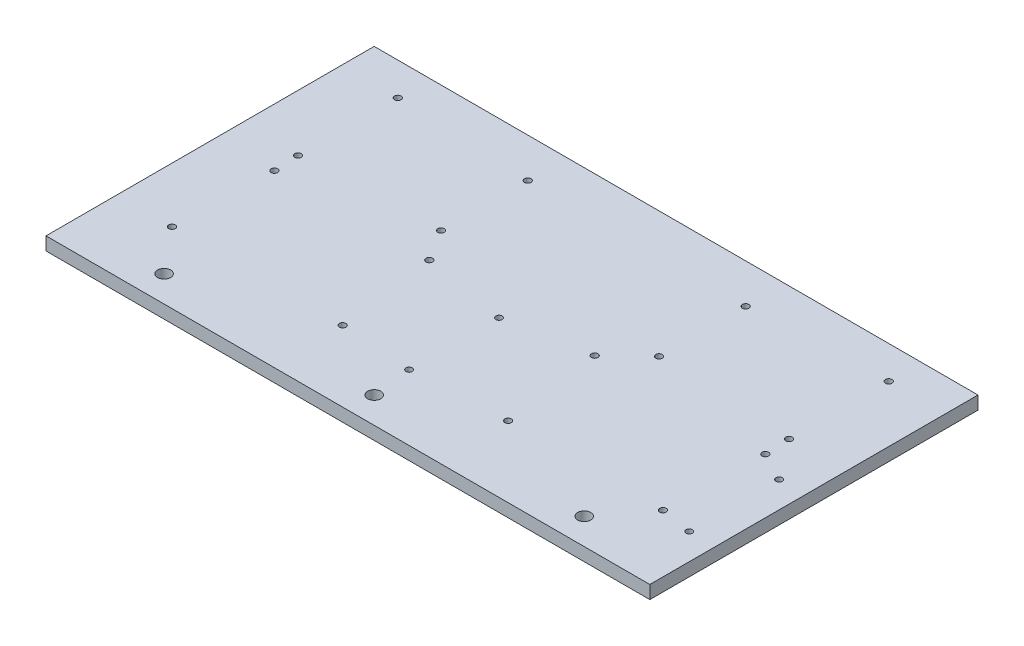
SolidWorks part; units mm, degrees
ref_plane "Front Plane" through (0, 0, 0) normal (0, 0, 1) x (1, 0, 0)
ref_plane "Top Plane" through (0, 0, 0) normal (0, 1, 0) x (1, 0, 0)
ref_plane "Right Plane" through (0, 0, 0) normal (1, 0, 0) x (0, 0, -1)
sketch "Sketch1" plane through (0, 0, 0) normal (0, 1, 0) x (1, 0, 0)
  line L1 (0, 0) -> (292.1, 0)
  line L2 (0, 0) -> (0, 158.75)
  line L3 (0, 158.75) -> (292.1, 158.75)
  line L4 (292.1, 0) -> (292.1, 158.75)
  dimension "D1" = 292.1
  dimension "D2" = 158.75
extrude "Boss-Extrude1" add sketch "Sketch1" along normal blind 6.35
sketch "Sketch2" plane through (0, 6.35, 0) normal (0, 1, 0) x (1, 0, 0)
  line L0 (0, 25.4) -> (292.1, 25.4) construction
  line L1 (0, 12.7) -> (292.1, 12.7) construction
  line L2 (146.05, 0) -> (146.05, 158.75) construction
  line L4 (0, 158.75) -> (0, 0)
  line L5 (0, 0) -> (292.1, 0)
  line L6 (292.1, 0) -> (292.1, 158.75)
  line L7 (292.1, 158.75) -> (0, 158.75)
  line L8 (0, 158.75) -> (0, 0) construction
  line L9 (0, 0) -> (292.1, 0) construction
  line L10 (292.1, 0) -> (292.1, 158.75) construction
  line L11 (292.1, 158.75) -> (0, 158.75) construction
  circle A0 centre (146.05, 12.7) radius 3.175
  circle A1 centre (247.65, 12.7) radius 3.175
  circle A2 centre (44.45, 12.7) radius 3.175
  dimension "D6" = 6.35
  dimension "D7" = 6.35
  dimension "D8" = 6.35
  dimension "D2" = 25.4
  dimension "D3" = 12.7
  dimension "D4" = 101.6
  dimension "D5" = 101.6
  dimension "D1" = 0
extrude "Cut-Extrude2" cut sketch "Sketch2" against normal blind 6.35
sketch "Sketch4" plane through (0, 6.35, 0) normal (0, 1, 0) x (1, 0, 0)
  line L4 (279.4, 85.09) -> (177.8, 85.09)
  line L5 (177.8, 85.09) -> (177.8, 31.75)
  line L6 (177.8, 31.75) -> (279.4, 31.75)
  line L7 (279.4, 31.75) -> (279.4, 85.09)
  line L8 (279.4, 85.09) -> (177.8, 85.09) construction
  line L9 (177.8, 85.09) -> (177.8, 31.75) construction
  line L10 (177.8, 31.75) -> (279.4, 31.75) construction
  line L11 (279.4, 31.75) -> (279.4, 85.09) construction
  line L160 (114.3, 31.75) -> (114.3, 85.09)
  line L161 (114.3, 85.09) -> (12.7, 85.09)
  line L162 (12.7, 85.09) -> (12.7, 31.75)
  line L163 (12.7, 31.75) -> (114.3, 31.75)
  line L164 (114.3, 31.75) -> (114.3, 85.09) construction
  line L165 (114.3, 85.09) -> (12.7, 85.09) construction
  line L166 (12.7, 85.09) -> (12.7, 31.75) construction
  line L167 (12.7, 31.75) -> (114.3, 31.75) construction
  circle A1 centre (182.88, 82.55) radius 1.5875
  circle A2 centre (182.88, 82.55) radius 1.5875
  circle A3 centre (189.23, 34.29) radius 1.5875
  circle A4 centre (189.23, 34.29) radius 1.5875
  circle A5 centre (265.43, 82.55) radius 1.5875
  circle A6 centre (265.43, 82.55) radius 1.5875
  circle A7 centre (264.16, 34.29) radius 1.5875
  circle A8 centre (264.16, 34.29) radius 1.5875
  circle A9 centre (264.795, 142.875) radius 1.5875
  circle A10 centre (264.795, 142.875) radius 1.5875
  circle A11 centre (264.795, 94.615) radius 1.5875
  circle A12 centre (264.795, 94.615) radius 1.5875
  circle A13 centre (198.755, 97.79) radius 1.5875
  circle A14 centre (198.755, 97.79) radius 1.5875
  circle A15 centre (198.755, 139.7) radius 1.5875
  circle A16 centre (198.755, 139.7) radius 1.5875
  circle A313 centre (102.87, 82.55) radius 1.5875
  circle A314 centre (102.87, 82.55) radius 1.5875
  circle A315 centre (109.22, 34.29) radius 1.5875
  circle A316 centre (109.22, 34.29) radius 1.5875
  circle A317 centre (26.67, 34.29) radius 1.5875
  circle A318 centre (26.67, 34.29) radius 1.5875
  circle A319 centre (27.94, 82.55) radius 1.5875
  circle A320 centre (27.94, 82.55) radius 1.5875
  circle A321 centre (93.345, 139.7) radius 1.5875
  circle A322 centre (93.345, 139.7) radius 1.5875
  circle A323 centre (93.345, 97.79) radius 1.5875
  circle A324 centre (93.345, 97.79) radius 1.5875
  circle A325 centre (27.305, 142.875) radius 1.5875
  circle A326 centre (27.305, 142.875) radius 1.5875
  circle A327 centre (27.305, 94.615) radius 1.5875
  circle A328 centre (27.305, 94.615) radius 1.5875
  dimension "D1" = 0
  dimension "D2" = 0
  dimension "D3" = 0
  dimension "D4" = 0
  dimension "D5" = 0
  dimension "D6" = 0
  dimension "D7" = 0
  dimension "D8" = 0
  dimension "D9" = 0
  dimension "D10" = 0
  dimension "D11" = 0
  dimension "D12" = 0
  dimension "D13" = 0
  dimension "D14" = 0
  dimension "D15" = 0
  dimension "D16" = 0
  dimension "D17" = 0
  dimension "D18" = 0
extrude "Cut-Extrude3" cut sketch "Sketch4" against normal through all
sketch "Sketch5" plane through (0, 6.35, 0) normal (0, 1, 0) x (1, 0, 0)
  line L0 (0, 0) -> (292.1, 0) construction
  line L1 (279.4, 31.75) -> (143.9, 31.75) construction
  line L2 (279.4, 31.75) -> (279.4, 75.25) construction
  line L3 (279.4, 75.25) -> (143.9, 75.25) construction
  line L4 (143.9, 31.75) -> (143.9, 75.25) construction
  line L5 (292.1, 0) -> (292.1, 158.75) construction
  circle A0 centre (279.4, 31.75) radius 1.525
  circle A1 centre (279.4, 75.25) radius 1.525
  circle A2 centre (143.9, 75.25) radius 1.525
  circle A3 centre (143.9, 31.75) radius 1.525
  dimension "D3" = 3.05
  dimension "D1" = 43.5
  dimension "D2" = 135.5
  dimension "D4" = 31.75
  dimension "D5" = 12.7
extrude "Cut-Extrude4" cut sketch "Sketch5" against normal through all
equation "\"D5@Sketch2\"=\"D4@Sketch2\""
equation "\"D7@Sketch2\"=\"D6@Sketch2\""
equation "\"D8@Sketch2\"=\"D7@Sketch2\""
equation "\"D4@Sketch5\"=1.25*25.4"
